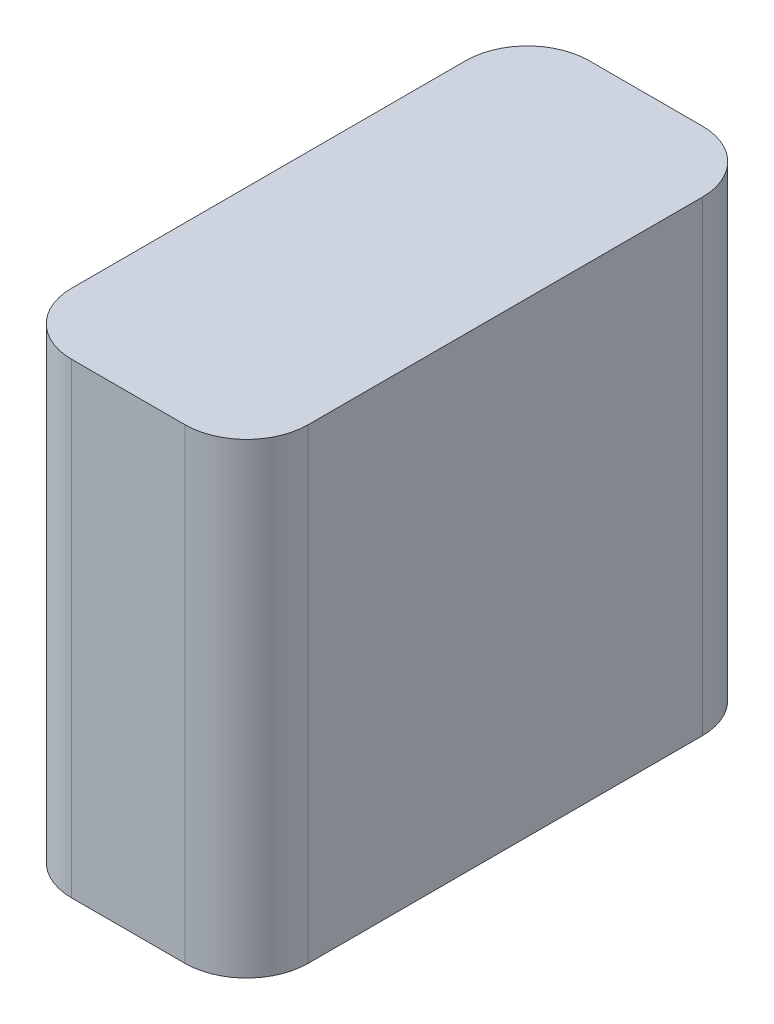
SolidWorks part; units mm, degrees
ref_plane "Front Plane" through (0, 0, 0) normal (0, 0, 1) x (1, 0, 0)
ref_plane "Top Plane" through (0, 0, 0) normal (0, 1, 0) x (1, 0, 0)
ref_plane "Right Plane" through (0, 0, 0) normal (1, 0, 0) x (0, 0, -1)
sketch "Sketch1" plane through (0, 0, 0) normal (0, 1, 0) x (1, 0, 0)
  line L1 (7.4994, 0) -> (21.2661, 0)
  line L2 (0, -7.4994) -> (0, -55.4291)
  line L3 (7.4994, -62.9285) -> (21.2661, -62.9285)
  line L4 (28.7655, -7.4994) -> (28.7655, -55.4291)
  arc A0 (0, -55.4291) -> (7.4994, -62.9285) centre (7.4994, -55.4291) ccw
  arc A1 (21.2661, -62.9285) -> (28.7655, -55.4291) centre (21.2662, -55.4291) ccw
  arc A2 (21.2661, 0) -> (28.7655, -7.4994) centre (21.2661, -7.4993) cw
  arc A3 (7.4994, 0) -> (0, -7.4994) centre (7.4993, -7.4993) ccw
  point P7 (0, -62.9285)
  point P10 (28.7655, -62.9285)
  point P15 (0, 0)
  dimension "D3" = 7.4993
  dimension "D1" = 28.7655
  dimension "D2" = 62.9285
extrude "Boss-Extrude1" add sketch "Sketch1" along normal blind 56.7436
